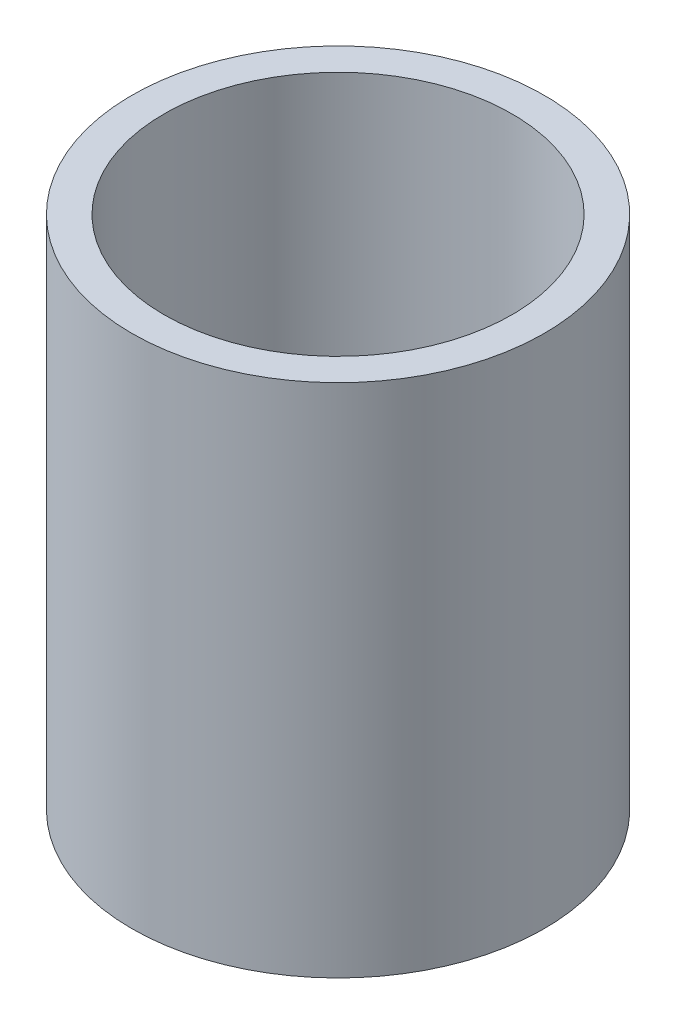
SolidWorks part; units mm, degrees
ref_plane "Front Plane" through (0, 0, 0) normal (0, 0, 1) x (1, 0, 0)
ref_plane "Top Plane" through (0, 0, 0) normal (0, 1, 0) x (1, 0, 0)
ref_plane "Right Plane" through (0, 0, 0) normal (1, 0, 0) x (0, 0, -1)
sketch "Sketch1" plane through (0, 0, 0) normal (0, 1, 0) x (1, 0, 0)
  circle A0 centre (0, 0) radius 20.32
  dimension "D1" = 40.64
extrude "Boss-Extrude1" add sketch "Sketch1" along normal blind 50.8
shell "Shell1" thickness 3.175
sketch "Sketch2" plane through (0, 3.175, 0) normal (0, 1, 0) x (1, 0, 0)
  circle A0 centre (0, 0) radius 4.064
  dimension "D1" = 8.128
extrude "Cut-Extrude1" cut sketch "Sketch2" along normal through all and the other way blind 46.482
